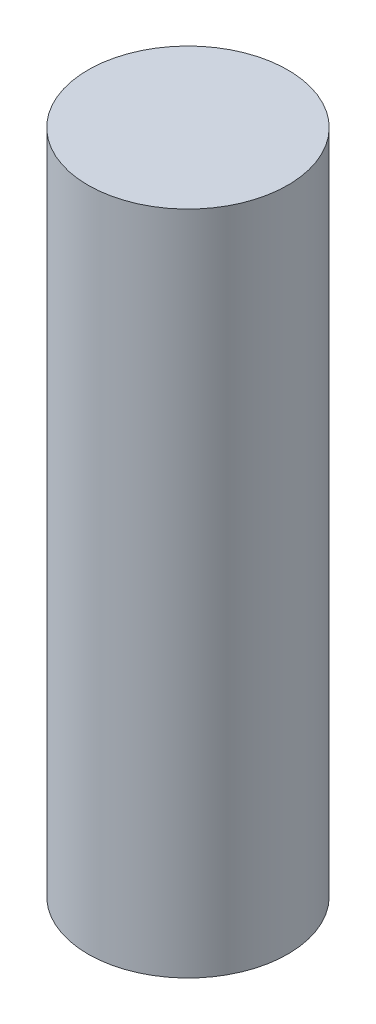
SolidWorks part; units mm, degrees
material "铸造合金钢"
ref_plane "前视基准面" through (0, 0, 0) normal (0, 0, 1) x (1, 0, 0)
ref_plane "上视基准面" through (0, 0, 0) normal (0, 1, 0) x (1, 0, 0)
ref_plane "右视基准面" through (0, 0, 0) normal (1, 0, 0) x (0, 0, -1)
other "Configuration Table"
sketch "草图1" plane through (0, 0, 0) normal (0, 1, 0) x (1, 0, 0)
  circle A0 centre (0, 0) radius 3
  dimension "D1" = 6
extrude "凸台-拉伸1" add sketch "草图1" along normal blind 20
